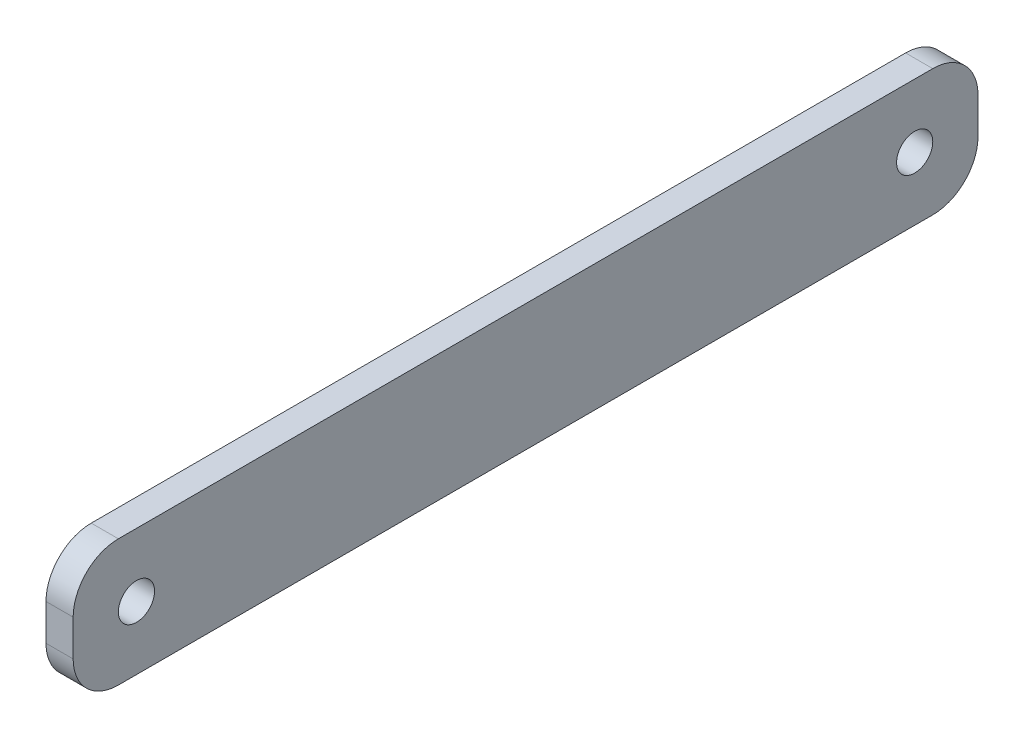
SolidWorks part; units mm, degrees
ref_plane "Front Plane" through (0, 0, 0) normal (0, 0, 1) x (1, 0, 0)
ref_plane "Top Plane" through (0, 0, 0) normal (0, 1, 0) x (1, 0, 0)
ref_plane "Right Plane" through (0, 0, 0) normal (1, 0, 0) x (0, 0, -1)
sketch "Sketch2" plane through (0, 0, 0) normal (1, 0, 0) x (0, 0, -1)
  line L1 (0, 0) -> (100, 0)
  line L2 (0, 0) -> (0, 14)
  line L3 (0, 14) -> (100, 14)
  line L4 (100, 0) -> (100, 14)
  circle A0 centre (7, 7) radius 2
  circle A1 centre (93, 7) radius 2
  dimension "D1" = 4
  dimension "D2" = 4
  dimension "D3" = 100
  dimension "D4" = 14
  dimension "D5" = 7
  dimension "D6" = 7
  dimension "D7" = 7
  dimension "D8" = 7
extrude "Boss-Extrude2" add sketch "Sketch2" along normal blind 3
fillet "Fillet1" radius 5 4 edges at (1.5, 0, 0) (1.5, 14, 0) (1.5, 0, -100) (1.5, 14, -100)
